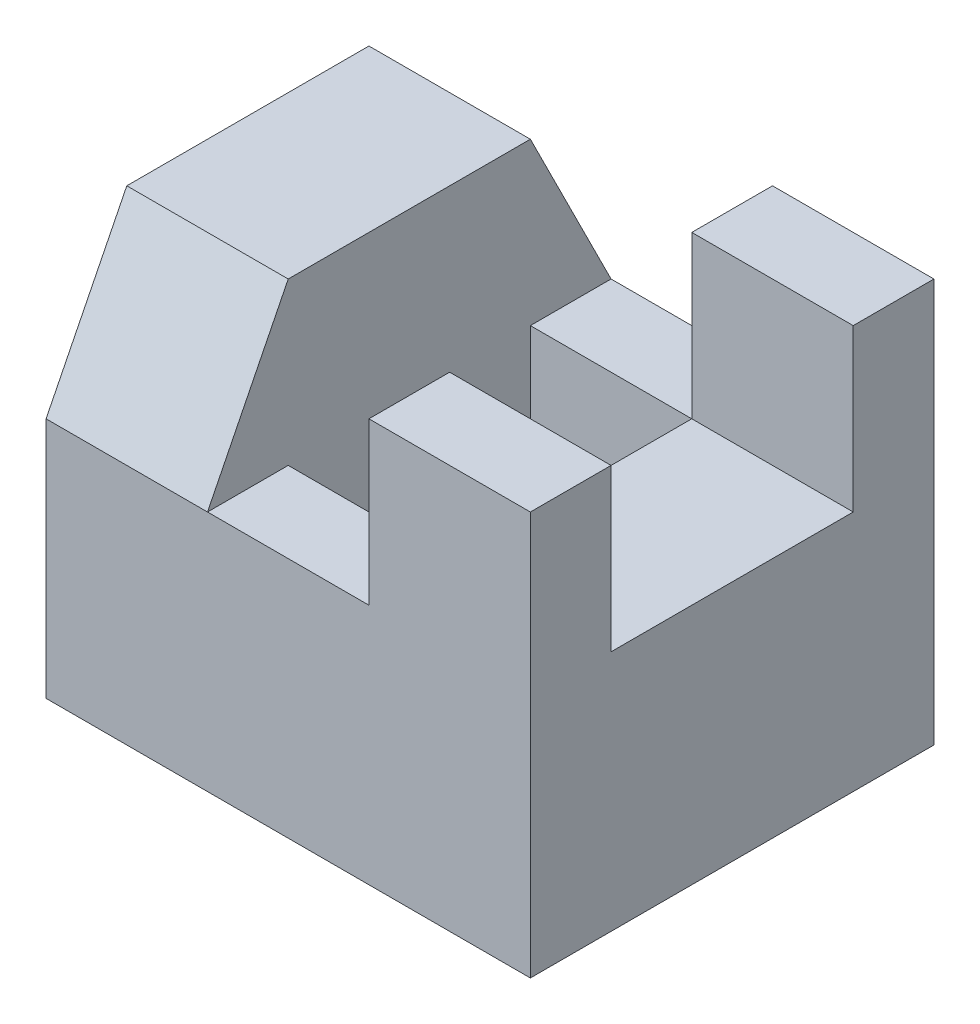
SolidWorks part; units mm, degrees
ref_plane "Front Plane" through (0, 0, 0) normal (0, 0, 1) x (1, 0, 0)
ref_plane "Top Plane" through (0, 0, 0) normal (0, 1, 0) x (1, 0, 0)
ref_plane "Right Plane" through (0, 0, 0) normal (1, 0, 0) x (0, 0, -1)
sketch "Sketch1" plane through (0, 0, 0) normal (0, 0, 1) x (1, 0, 0)
  line L1 (0, 0) -> (30, 0)
  line L2 (0, 0) -> (0, 25)
  line L3 (0, 25) -> (30, 25)
  line L4 (30, 0) -> (30, 25)
  dimension "D1" = 25
  dimension "D2" = 30
extrude "Boss-Extrude1" add sketch "Sketch1" along normal blind 25
sketch "Sketch2" plane through (0, 0, 0) normal (-1, 0, 0) x (0, 0, 1)
  line L0 (0, 15) -> (5, 25)
  line L1 (0, 25) -> (0, 0) construction
  line L2 (25, 25) -> (0, 25) construction
  line L3 (5, 25) -> (0, 25)
  line L4 (0, 25) -> (0, 15)
  line L5 (25, 25) -> (20, 25)
  line L6 (20, 25) -> (25, 15)
  line L7 (25, 25) -> (25, 0) construction
  line L8 (25, 15) -> (25, 25)
  point P10 (0, 20)
  dimension "D1" = 10
  dimension "D2" = 5
  dimension "D3" = 5
  dimension "D4" = 10
extrude "Cut-Extrude1" cut sketch "Sketch2" against normal blind 10
sketch "Sketch3" plane through (0, 25, 0) normal (0, 1, 0) x (1, 0, 0)
  line L0 (30, -25) -> (10, -25) construction
  line L1 (10, 0) -> (20, 0)
  line L2 (10, 0) -> (10, -25)
  line L3 (10, -25) -> (20, -25)
  line L4 (20, 0) -> (20, -25)
extrude "Cut-Extrude3" cut sketch "Sketch3" against normal blind 10
sketch "Sketch5" plane through (0, 15, 0) normal (0, 1, 0) x (1, 0, 0)
  line L0 (20, -25) -> (20, 0) construction
  line L1 (10, -5) -> (20, -5)
  line L2 (10, -5) -> (10, -20)
  line L3 (10, -20) -> (20, -20)
  line L4 (20, -5) -> (20, -20)
  dimension "D1" = 15
extrude "Cut-Extrude4" cut sketch "Sketch5" against normal blind 30
sketch "Sketch6" plane through (0, 25, 0) normal (0, 1, 0) x (1, 0, 0)
  line L0 (30, -25) -> (30, 0) construction
  line L1 (20, -5) -> (30, -5)
  line L2 (20, -5) -> (20, -20)
  line L3 (20, -20) -> (30, -20)
  line L4 (30, -5) -> (30, -20)
  dimension "D1" = 15
extrude "Cut-Extrude5" cut sketch "Sketch6" against normal blind 10
